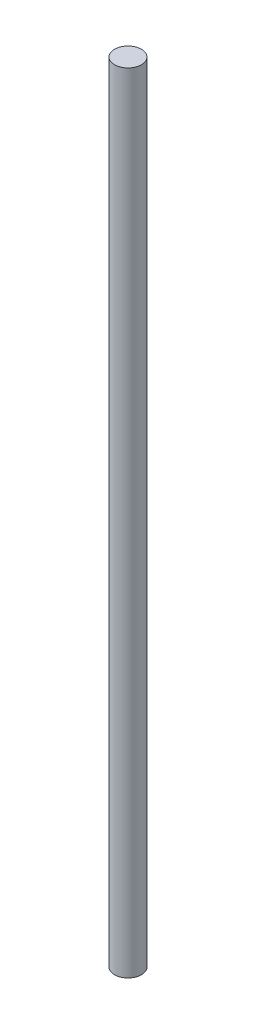
SolidWorks part; units mm, degrees
ref_plane "Front Plane" through (0, 0, 0) normal (0, 0, 1) x (1, 0, 0)
ref_plane "Top Plane" through (0, 0, 0) normal (0, 1, 0) x (1, 0, 0)
ref_plane "Right Plane" through (0, 0, 0) normal (1, 0, 0) x (0, 0, -1)
sketch "Sketch1" plane through (0, 0, 0) normal (0, 1, 0) x (1, 0, 0)
  circle A0 centre (0, 0) radius 12.5
  dimension "D1" = 25
extrude "Boss-Extrude1" add sketch "Sketch1" along normal blind 732.5
